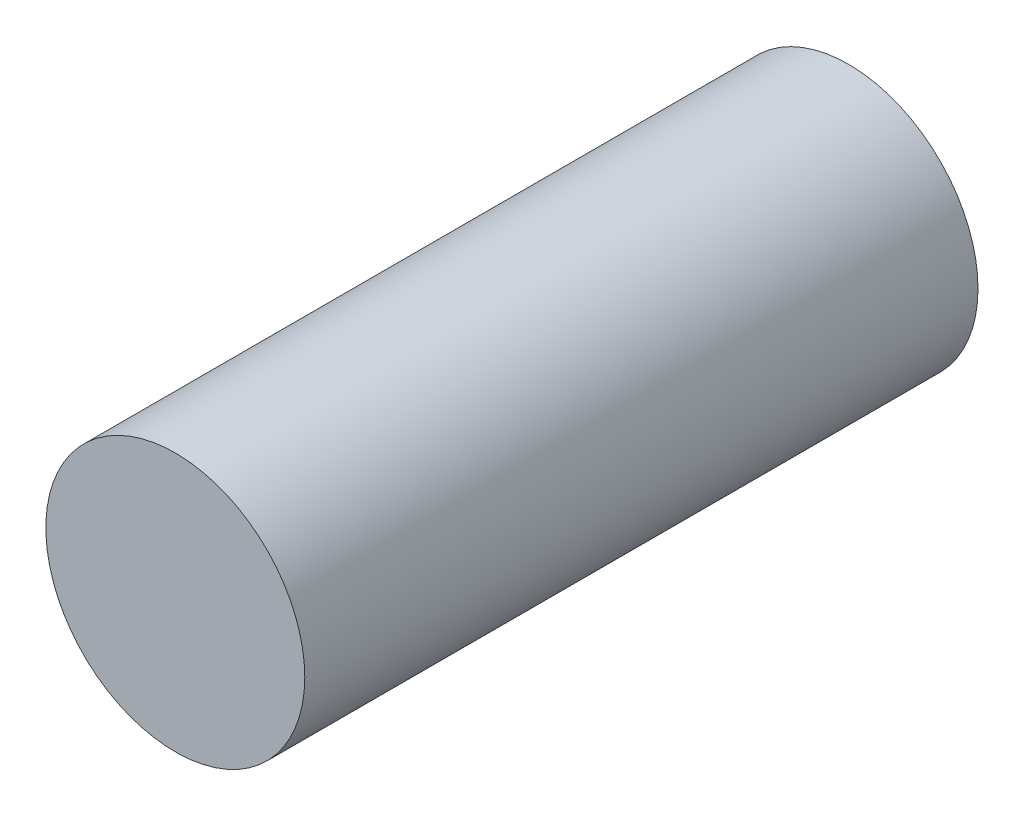
SolidWorks part; units mm, degrees
ref_plane "Front Plane" through (0, 0, 0) normal (0, 0, 1) x (1, 0, 0)
ref_plane "Top Plane" through (0, 0, 0) normal (0, 1, 0) x (1, 0, 0)
ref_plane "Right Plane" through (0, 0, 0) normal (1, 0, 0) x (0, 0, -1)
sketch "Sketch1" plane through (0, 0, 0) normal (0, 0, 1) x (1, 0, 0)
  circle A0 centre (0, 0) radius 5
  dimension "D1" = 10
extrude "Boss-Extrude1" add sketch "Sketch1" along normal blind 26
